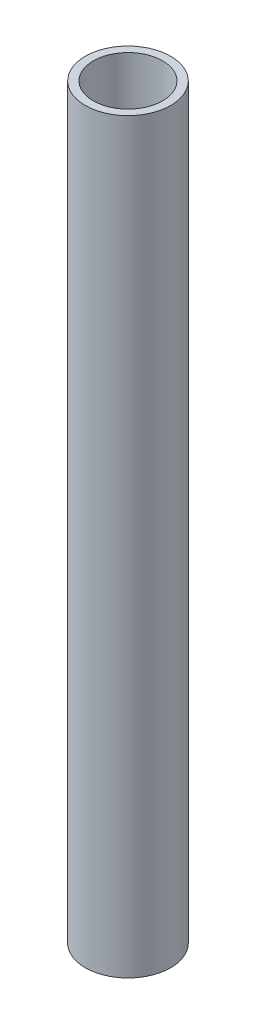
SolidWorks part; units mm, degrees
ref_plane "Front Plane" through (0, 0, 0) normal (0, 0, 1) x (1, 0, 0)
ref_plane "Top Plane" through (0, 0, 0) normal (0, 1, 0) x (1, 0, 0)
ref_plane "Right Plane" through (0, 0, 0) normal (1, 0, 0) x (0, 0, -1)
sketch "Sketch1" plane through (0, 0, 0) normal (0, 1, 0) x (1, 0, 0)
  circle A0 centre (0, 0) radius 8
  circle A1 centre (0, 0) radius 6.5
extrude "Boss-Extrude1" add sketch "Sketch1" along normal blind 140
